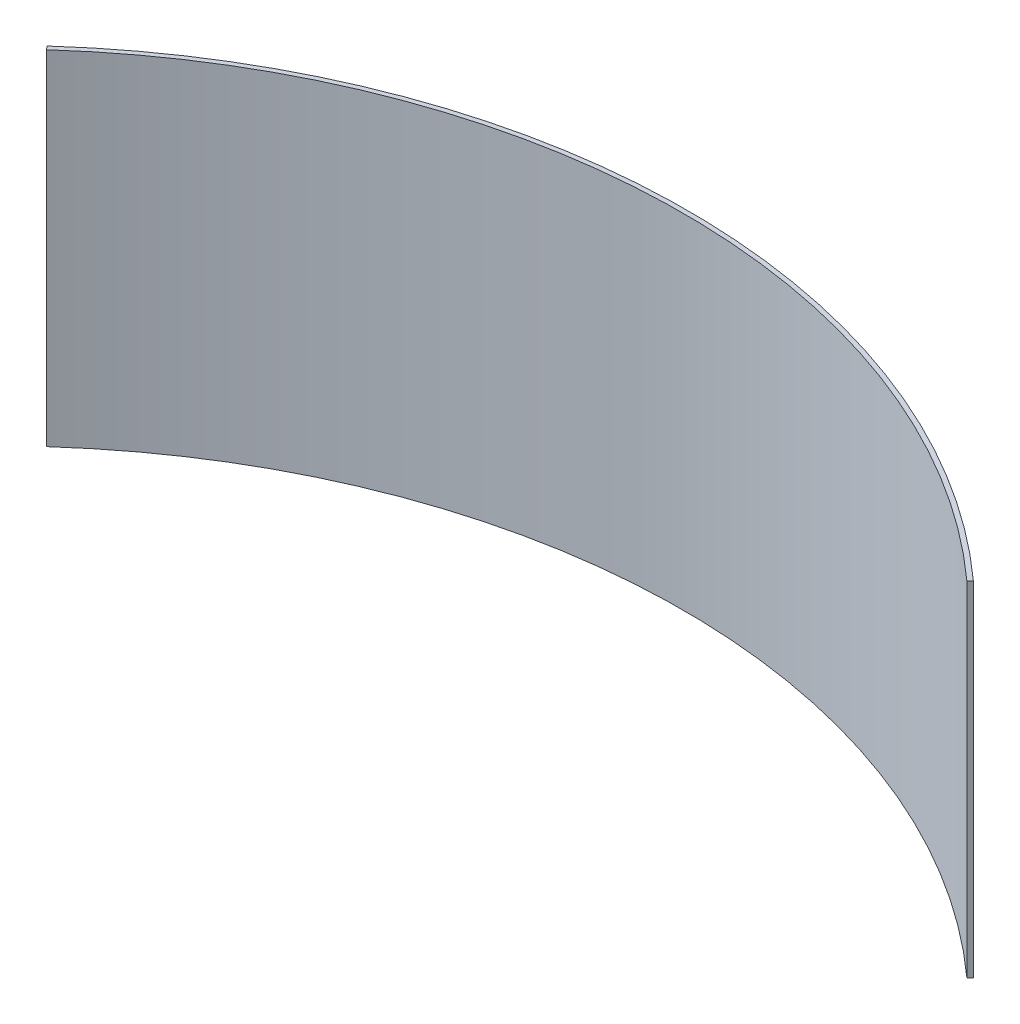
SolidWorks part; units mm, degrees
ref_plane "Front Plane" through (0, 0, 0) normal (0, 0, 1) x (1, 0, 0)
ref_plane "Top Plane" through (0, 0, 0) normal (0, 1, 0) x (1, 0, 0)
ref_plane "Right Plane" through (0, 0, 0) normal (1, 0, 0) x (0, 0, -1)
sketch "Sketch1" plane through (0, 0, 0) normal (0, 1, 0) x (1, 0, 0)
  line L0 (0, 0) -> (0, 36006.289) construction
  line L1 (0, 0) -> (36006.289, 0) construction
  line L2 (-20.0805, 22.2884) -> (20.0805, 22.2884) construction
  line L3 (-20.0805, 22.2884) -> (0, 0) construction
  line L4 (0, 0) -> (20.0805, 22.2884) construction
  line L5 (-20.2144, 22.437) -> (-20.0805, 22.2884)
  line L6 (20.2144, 22.437) -> (20.0805, 22.2884)
  arc A0 (20.0805, 22.2884) -> (-20.0805, 22.2884) centre (0, 0) ccw
  circle A1 centre (0, 0) radius 30 construction
  arc A2 (20.2144, 22.437) -> (-20.2144, 22.437) centre (0, 0) ccw
  point P10 (0, 22.2884)
  dimension "D1" = 30
  dimension "D2" = 60
  dimension "D3" = 84.034
  dimension "D4" = 40.161
  dimension "D5" = 0.2
extrude "Boss-Extrude1" add sketch "Sketch1" along normal mid plane 15
equation "\"deg\"= ( 360 * \"ant_length\" ) / ( 2 * pi * \"bend R\" )"
equation "\"D3@Sketch1\"=\"deg\""
equation "\"bend R\"= ( 60 - 0 ) / 2"
equation "\"ant_length\"= 44"
equation "\"D1@Sketch1\"=\"bend R\""
